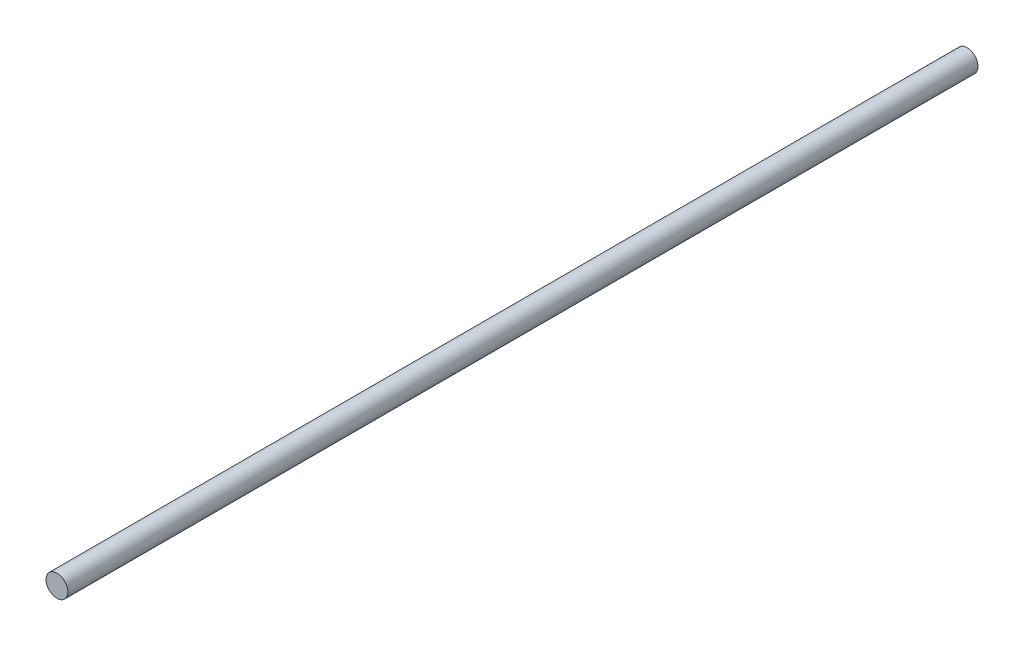
SolidWorks part; units mm, degrees
ref_plane "Plano frontal" through (0, 0, 0) normal (0, 0, 1) x (1, 0, 0)
ref_plane "Plano superior" through (0, 0, 0) normal (0, 1, 0) x (1, 0, 0)
ref_plane "Plano direito" through (0, 0, 0) normal (1, 0, 0) x (0, 0, -1)
sketch "Esboço1" plane through (0, 0, 0) normal (0, 0, 1) x (1, 0, 0)
  circle A0 centre (0, 0) radius 3
  dimension "D1" = 6
extrude "Ressalto-extrusão1" add sketch "Esboço1" along normal blind 250
